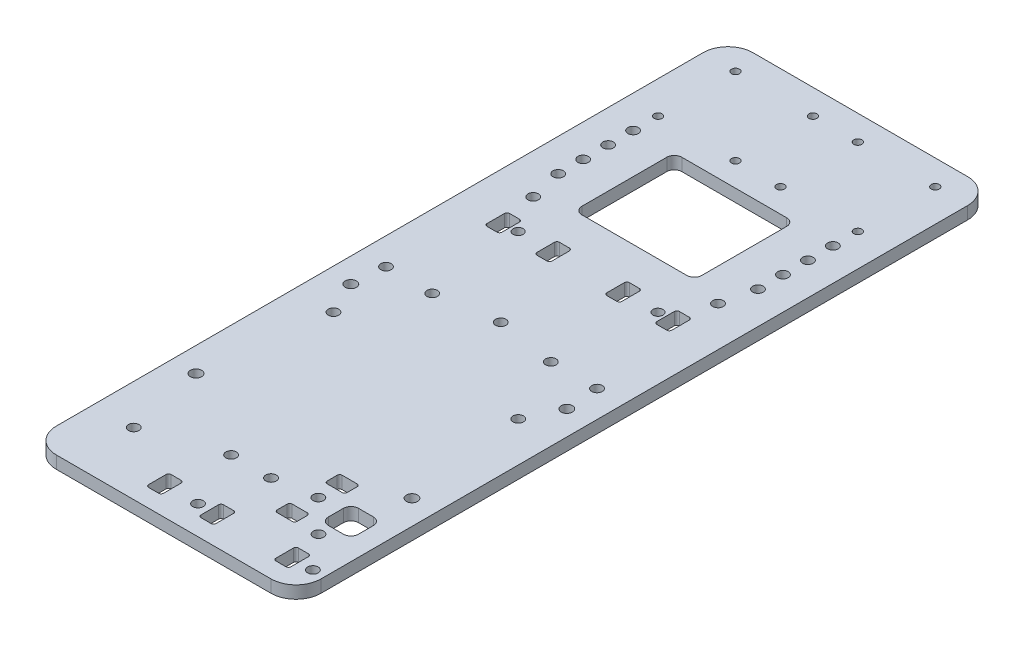
SolidWorks part; units mm, degrees
material "Thornel Mat VMA"
ref_plane "前视基准面" through (0, 0, 0) normal (0, 0, 1) x (1, 0, 0)
ref_plane "上视基准面" through (0, 0, 0) normal (0, 1, 0) x (1, 0, 0)
ref_plane "右视基准面" through (0, 0, 0) normal (1, 0, 0) x (0, 0, -1)
sketch "草图1" plane through (0, 0, 0) normal (0, 1, 0) x (1, 0, 0)
  line L0 (0, -55) -> (0, 55) construction
  line L1 (-43, -137) -> (43, -137)
  line L2 (-53, -127) -> (-53, 132)
  line L3 (-43, 142) -> (43, 142)
  line L4 (53, -127) -> (53, 132)
  line L8 (21, 91.5) -> (-21, 91.5)
  line L9 (24, 88.5) -> (24, 54.5)
  line L10 (21, 51.5) -> (-21, 51.5)
  line L11 (-24, 88.5) -> (-24, 54.5)
  circle A15 centre (-40, 132) radius 1.6
  circle A16 centre (-9, 132) radius 1.6
  circle A17 centre (-9, 101) radius 1.6
  circle A18 centre (-40, 101) radius 1.6
  circle A19 centre (9, 101) radius 1.6
  circle A20 centre (40, 101) radius 1.6
  circle A21 centre (9, 132) radius 1.6
  circle A22 centre (40, 132) radius 1.6
  arc A23 (-43, 142) -> (-53, 132) centre (-43, 132) ccw
  arc A24 (43, 142) -> (53, 132) centre (43, 132) cw
  arc A25 (53, -127) -> (43, -137) centre (43, -127) cw
  arc A26 (-43, -137) -> (-53, -127) centre (-43, -127) cw
  circle A27 centre (-37, -112) radius 2.1
  circle A28 centre (-37, -32) radius 2.1
  circle A29 centre (-37, 48) radius 2.1
  circle A30 centre (37, -112) radius 2.1
  circle A31 centre (37, -32) radius 2.1
  circle A32 centre (37, 48) radius 2.1
  arc A37 (24, 54.5) -> (21, 51.5) centre (21, 54.5) cw
  arc A38 (21, 91.5) -> (24, 88.5) centre (21, 88.5) cw
  arc A39 (-21, 91.5) -> (-24, 88.5) centre (-21, 88.5) ccw
  arc A40 (-21, 51.5) -> (-24, 54.5) centre (-21, 54.5) cw
  circle A58 centre (-40, 91) radius 2.1
  circle A59 centre (-40, 81) radius 2.1
  circle A60 centre (-40, 71) radius 2.1
  circle A61 centre (-40, 61) radius 2.1
  circle A62 centre (40, 61) radius 2.1
  circle A63 centre (40, 71) radius 2.1
  circle A64 centre (40, 81) radius 2.1
  circle A65 centre (40, 91) radius 2.1
  circle A66 centre (-42.25, -5.7) radius 2.1
  circle A67 centre (-23.75, -5.7) radius 2.1
  circle A68 centre (23.75, -5.7) radius 2.1
  circle A69 centre (42.25, -5.7) radius 2.1
  point P0 (0, 0)
  point P12 (0, 91.5)
  line B0 (-36, 37.5) -> (-32, 37.5)
  line B1 (-37, 36.5) -> (-37, 29.5)
  line B2 (-36, 28.5) -> (-32, 28.5)
  line B3 (-31, 36.5) -> (-31, 29.5)
  line B4 (-16, 37.5) -> (-12, 37.5)
  line B5 (-17, 36.5) -> (-17, 29.5)
  line B6 (-16, 28.5) -> (-12, 28.5)
  line B7 (-11, 36.5) -> (-11, 29.5)
  line B8 (37, 36.5) -> (37, 29.5)
  line B9 (36, 28.5) -> (32, 28.5)
  line B10 (31, 36.5) -> (31, 29.5)
  line B11 (36, 37.5) -> (32, 37.5)
  line B12 (17, 36.5) -> (17, 29.5)
  line B13 (16, 28.5) -> (12, 28.5)
  line B14 (11, 36.5) -> (11, 29.5)
  line B15 (16, 37.5) -> (12, 37.5)
  circle B16 centre (-28, 32.95) radius 2
  circle B17 centre (28, 32.95) radius 2
  arc B18 (17, 29.5) -> (16, 28.5) centre (16, 29.5) cw
  arc B19 (12, 28.5) -> (11, 29.5) centre (12, 29.5) cw
  arc B20 (11, 36.5) -> (12, 37.5) centre (12, 36.5) cw
  arc B21 (17, 36.5) -> (16, 37.5) centre (16, 36.5) ccw
  arc B22 (31, 36.5) -> (32, 37.5) centre (32, 36.5) cw
  arc B23 (37, 36.5) -> (36, 37.5) centre (36, 36.5) ccw
  arc B24 (37, 29.5) -> (36, 28.5) centre (36, 29.5) cw
  arc B25 (32, 28.5) -> (31, 29.5) centre (32, 29.5) cw
  arc B26 (-12, 37.5) -> (-11, 36.5) centre (-12, 36.5) cw
  arc B27 (-12, 28.5) -> (-11, 29.5) centre (-12, 29.5) ccw
  arc B28 (-17, 29.5) -> (-16, 28.5) centre (-16, 29.5) ccw
  arc B29 (-36, 37.5) -> (-37, 36.5) centre (-36, 36.5) ccw
  arc B30 (-16, 37.5) -> (-17, 36.5) centre (-16, 36.5) ccw
  arc B31 (-32, 28.5) -> (-31, 29.5) centre (-32, 29.5) ccw
  arc B32 (-32, 37.5) -> (-31, 36.5) centre (-32, 36.5) cw
  arc B33 (-37, 29.5) -> (-36, 28.5) centre (-36, 29.5) ccw
  dimension "D3" = 50.5
  dimension "D4" = 31
  dimension "D5" = 40
  dimension "D6" = 31
  dimension "D7" = 48
  dimension "D8" = 10
  dimension "D14" = 3.2
  dimension "D18" = 10
  dimension "D19" = 10
  dimension "D20" = 10
  dimension "D21" = 10
  dimension "D38" = 3
  dimension "D39" = 3
  dimension "D43" = 4.2
  dimension "D64" = 4.2
  dimension "D65" = 18.5
  dimension "D9" = 24
  dimension "D10" = 40
  dimension "D12" = 94
  dimension "D13" = 28
  dimension "D25" = 37
  dimension "D30" = 106
  dimension "D31" = 279
  dimension "D32" = 142
  dimension "D33" = 53
  dimension "D34" = 80
  dimension "D35" = 80
  dimension "D44" = 10
  dimension "D55" = 165.5
  dimension "D62" = 147.7
  dimension "D63" = 10.75
  dimension "D45" = 4
sketch_block_instance "块3-1"
sketch_block "块3" parameters "D1"=4, "D7"=1, "D2"=6, "D3"=9, "D4"=20, "D5"=6, "D6"=9
extrude "凸台-拉伸1" add sketch "草图1" along normal blind 5
sketch "草图2" plane through (0, 0, 0) normal (0, 1, 0) x (1, 0, 0)
  line L0 (-43, -137) -> (43, -137) construction
  point P1 (0, -49.8)
  circle B0 centre (-43.25, -80.8) radius 2.25
  circle B1 centre (43.25, -80.8) radius 2.25
  circle B2 centre (-43.25, -18.8) radius 2.25
  circle B3 centre (43.25, -18.8) radius 2.25
  line B4 (43.25, -18.8) -> (-43.25, -80.8) construction
  dimension "D1" = 43.25
  dimension "D2" = 87.2
sketch_block_instance "块2-1"
sketch_block "块2" parameters "D3"=4.5, "D1"=62, "D2"=86.5
extrude "切除-拉伸2" cut sketch "草图2" along normal blind 10
sketch "草图3" plane through (0, 0, 0) normal (0, 1, 0) x (1, 0, 0)
  line L0 (53, -127) -> (53, 132) construction
  line L1 (-43, -137) -> (43, -137) construction
  line B0 (37.78, -120.8) -> (41.78, -120.8)
  line B1 (7.78, -120.8) -> (11.78, -120.8)
  line B2 (6.78, -121.8) -> (6.78, -128.8)
  line B3 (7.78, -129.8) -> (11.78, -129.8)
  line B4 (12.78, -121.8) -> (12.78, -128.8)
  line B5 (36.78, -121.8) -> (36.78, -128.8)
  line B6 (37.78, -129.8) -> (41.78, -129.8)
  line B7 (42.78, -121.8) -> (42.78, -128.8)
  line B8 (21.28, -106.8) -> (27.28, -106.8)
  line B9 (20.28, -107.8) -> (20.28, -111.8)
  line B10 (21.28, -112.8) -> (27.28, -112.8)
  line B11 (28.28, -107.8) -> (28.28, -111.8)
  line B12 (21.28, -86.8) -> (27.28, -86.8)
  line B13 (20.28, -87.8) -> (20.28, -91.8)
  line B14 (21.28, -92.8) -> (27.28, -92.8)
  line B15 (28.28, -87.8) -> (28.28, -91.8)
  circle B16 centre (2.28, -125.5) radius 2.1
  circle B17 centre (48.28, -125.5) radius 2.1
  circle B18 centre (24.28, -99.3277) radius 2.1
  line B19 (24.28, -99.3277) -> (24.28, -157.4537) construction
  line B20 (-8.22, -121.8) -> (-8.22, -128.8)
  line B21 (-9.22, -129.8) -> (-13.22, -129.8)
  line B22 (-14.22, -121.8) -> (-14.22, -128.8)
  line B23 (-9.22, -120.8) -> (-13.22, -120.8)
  line B24 (2.28, -125.5) -> (48.28, -125.5) construction
  arc B25 (20.28, -91.8) -> (21.28, -92.8) centre (21.28, -91.8) ccw
  arc B26 (21.28, -86.8) -> (20.28, -87.8) centre (21.28, -87.8) ccw
  arc B27 (27.28, -86.8) -> (28.28, -87.8) centre (27.28, -87.8) cw
  arc B28 (27.28, -92.8) -> (28.28, -91.8) centre (27.28, -91.8) ccw
  arc B29 (36.78, -128.8) -> (37.78, -129.8) centre (37.78, -128.8) ccw
  arc B30 (41.78, -129.8) -> (42.78, -128.8) centre (41.78, -128.8) ccw
  arc B31 (41.78, -120.8) -> (42.78, -121.8) centre (41.78, -121.8) cw
  arc B32 (37.78, -120.8) -> (36.78, -121.8) centre (37.78, -121.8) ccw
  arc B33 (27.28, -112.8) -> (28.28, -111.8) centre (27.28, -111.8) ccw
  arc B34 (27.28, -106.8) -> (28.28, -107.8) centre (27.28, -107.8) cw
  arc B35 (21.28, -106.8) -> (20.28, -107.8) centre (21.28, -107.8) ccw
  arc B36 (20.28, -111.8) -> (21.28, -112.8) centre (21.28, -111.8) ccw
  arc B37 (7.78, -120.8) -> (6.78, -121.8) centre (7.78, -121.8) ccw
  arc B38 (11.78, -120.8) -> (12.78, -121.8) centre (11.78, -121.8) cw
  arc B39 (11.78, -129.8) -> (12.78, -128.8) centre (11.78, -128.8) ccw
  arc B40 (6.78, -128.8) -> (7.78, -129.8) centre (7.78, -128.8) ccw
  arc B41 (-8.22, -128.8) -> (-9.22, -129.8) centre (-9.22, -128.8) cw
  arc B42 (-8.22, -121.8) -> (-9.22, -120.8) centre (-9.22, -121.8) ccw
  arc B43 (-14.22, -121.8) -> (-13.22, -120.8) centre (-13.22, -121.8) cw
  arc B44 (-13.22, -129.8) -> (-14.22, -128.8) centre (-13.22, -128.8) cw
  dimension "D1" = 28.72
  dimension "D2" = 11.5
sketch_block_instance "块1-2"
sketch_block "块1" parameters "D1"=4.2, "D2"=4, "D12"=4, "D3"=46, "D4"=6, "D5"=6, "D6"=9, "D7"=6, "D8"=8, "D9"=6, "D10"=8, "D11"=6
extrude "切除-拉伸3" cut sketch "草图3" along normal blind 27
sketch "草图4" plane through (0, 0, 0) normal (0, 1, 0) x (1, 0, 0)
  line L0 (53, -127) -> (53, 132) construction
  line L1 (36, -95) -> (42, -95)
  line L2 (33, -98) -> (33, -104)
  line L3 (36, -107) -> (42, -107)
  line L4 (45, -98) -> (45, -104)
  line L5 (-43, -137) -> (43, -137) construction
  arc A1 (42, -95) -> (45, -98) centre (42, -98) cw
  arc A2 (42, -107) -> (45, -104) centre (42, -104) ccw
  arc A3 (33, -104) -> (36, -107) centre (36, -104) ccw
  arc A4 (36, -95) -> (33, -98) centre (36, -98) ccw
  point P10 (45, -95)
  point P13 (45, -107)
  point P18 (33, -95)
  dimension "D3" = 8
  dimension "D5" = 3
  dimension "D1" = 12
  dimension "D2" = 12
  dimension "D4" = 30
extrude "切除-拉伸4" cut sketch "草图4" along normal blind 20
sketch "草图5" plane through (0, 0, 0) normal (0, 1, 0) x (1, 0, 0)
  line L0 (-43, -137) -> (43, -137) construction
  line L1 (0, -2.75) -> (0, 2.75) construction
  circle A0 centre (0, -2) radius 2.1
  circle A1 centre (-8, -102) radius 2.1
  circle A2 centre (8, -102) radius 2.1
  dimension "D1" = 4.2
  dimension "D2" = 135
  dimension "D3" = 8
  dimension "D4" = 35
extrude "切除-拉伸5" cut sketch "草图5" along normal blind 20
equation "\"44。5\"=45.5"
